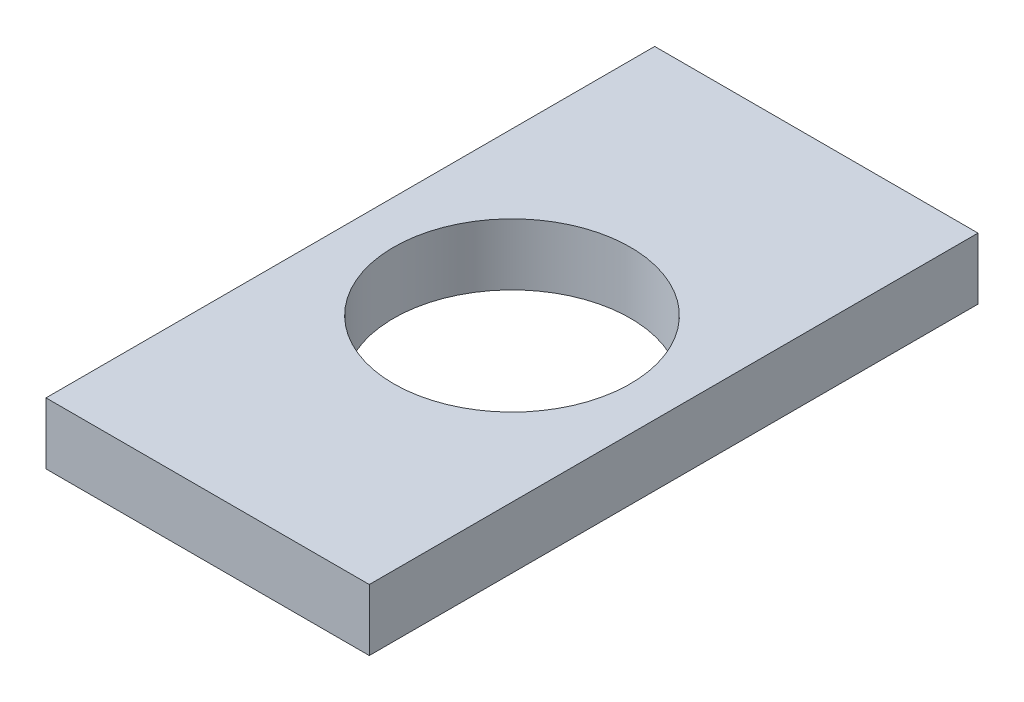
SolidWorks part; units mm, degrees
ref_plane "Front Plane" through (0, 0, 0) normal (0, 0, 1) x (1, 0, 0)
ref_plane "Top Plane" through (0, 0, 0) normal (0, 1, 0) x (1, 0, 0)
ref_plane "Right Plane" through (0, 0, 0) normal (1, 0, 0) x (0, 0, -1)
sketch "Sketch1" plane through (0, 0, 0) normal (0, 1, 0) x (1, 0, 0)
  line L1 (0, 0) -> (47.8, 0)
  line L2 (0, 0) -> (0, 90)
  line L3 (0, 90) -> (47.8, 90)
  line L4 (47.8, 0) -> (47.8, 90)
  circle A0 centre (23.9, 45) radius 17.5
  point P7 (23.9, 90)
  point P8 (0, 0)
  point P9 (0, 45)
  dimension "D3" = 35
  dimension "D1" = 47.8
  dimension "D2" = 90
extrude "Boss-Extrude1" add sketch "Sketch1" along normal blind 9.1
